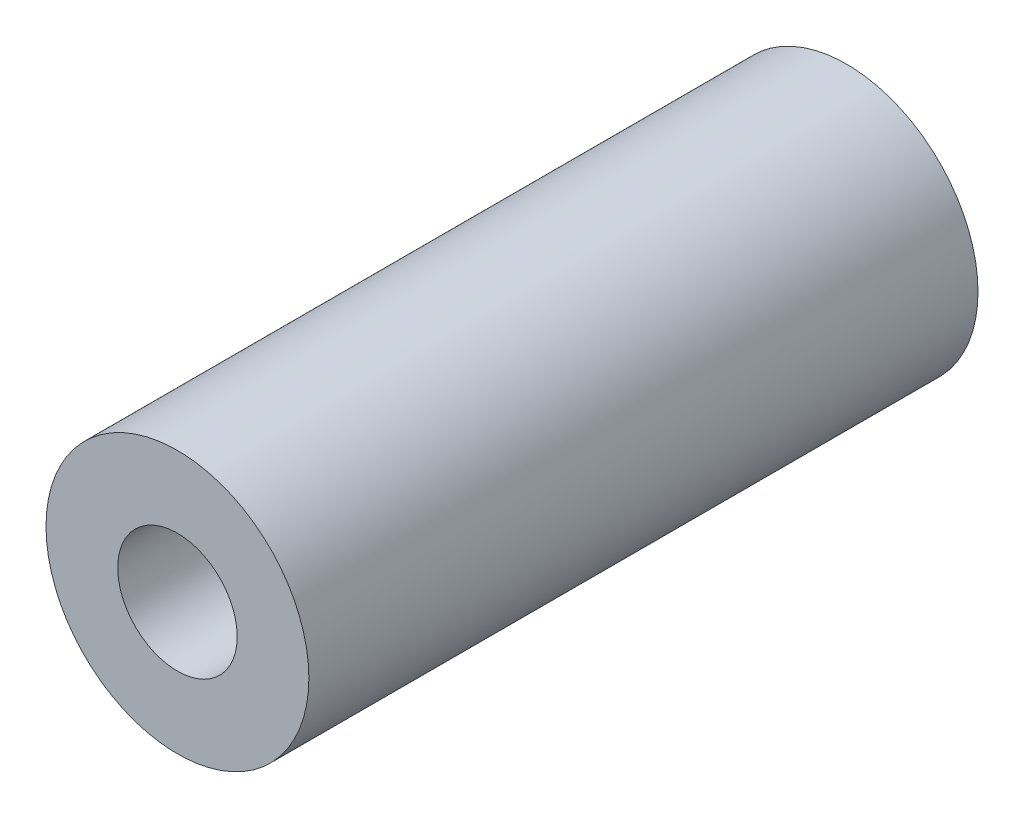
SolidWorks part; units mm, degrees
ref_plane "Alzado" through (0, 0, 0) normal (0, 0, 1) x (1, 0, 0)
ref_plane "Planta" through (0, 0, 0) normal (0, 1, 0) x (1, 0, 0)
ref_plane "Vista lateral" through (0, 0, 0) normal (1, 0, 0) x (0, 0, -1)
sketch "Croquis1" plane through (0, 0, 0) normal (0, 0, 1) x (1, 0, 0)
  line L1 (-6, 5) -> (6, 5)
  line L2 (-6, 5) -> (-6, -5)
  line L3 (-6, -5) -> (6, -5)
  line L4 (6, 5) -> (6, -5)
  line L5 (-6, 5) -> (6, -5) construction
  line L6 (-6, -5) -> (6, 5) construction
  circle A0 centre (0, 0) radius 11
  dimension "D1" = 22
  dimension "D2" = 12
  dimension "D3" = 10
extrude "Saliente-Extruir1" add sketch "Croquis1" along normal blind 26
sketch "Croquis3" plane through (0, 0, 26) normal (0, 0, 1) x (1, 0, 0)
  circle A0 centre (0, 0) radius 11
  circle A1 centre (0, 0) radius 8
  dimension "D1" = 22
  dimension "D2" = 16
extrude "Saliente-Extruir2" add sketch "Croquis3" along normal blind 30
sketch "Croquis5" plane through (0, 0, 56) normal (0, 0, 1) x (1, 0, 0)
  circle A0 centre (0, 0) radius 11
  circle A1 centre (0, 0) radius 5
  dimension "D1" = 22
  dimension "D2" = 10
extrude "Saliente-Extruir3" add sketch "Croquis5" against normal blind 15
